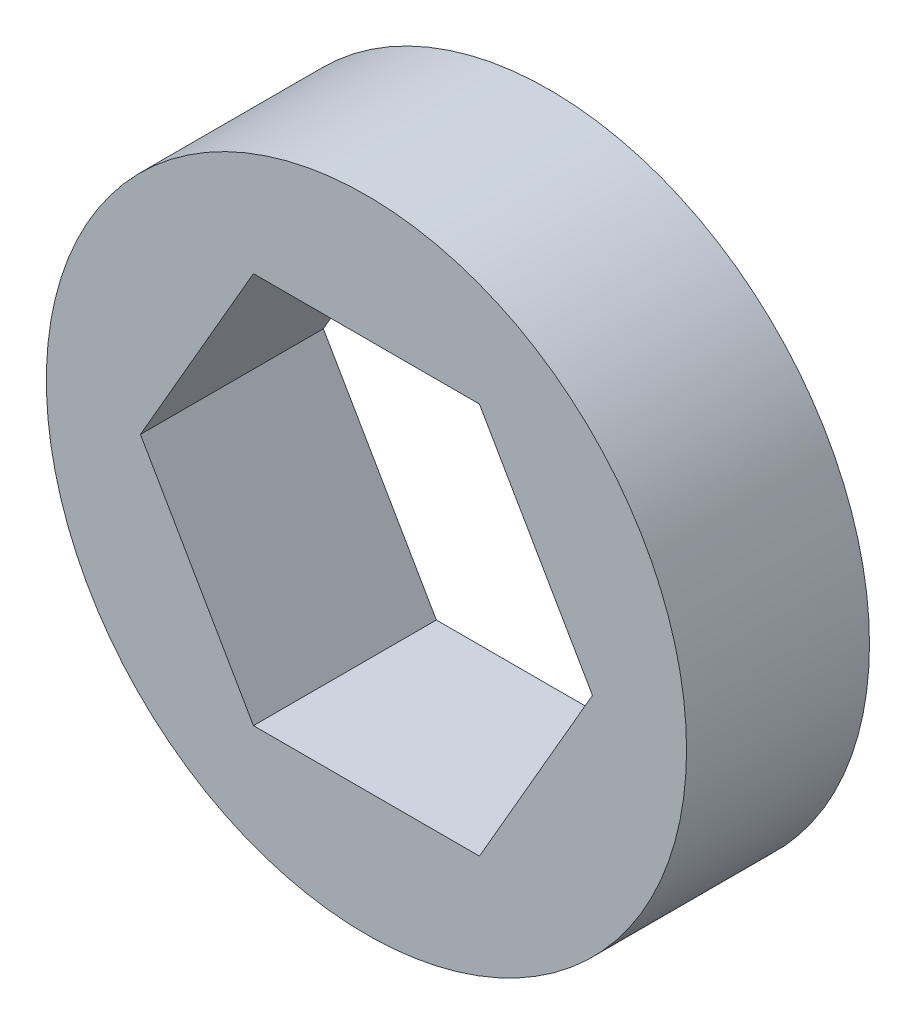
SolidWorks part; units mm, degrees
ref_plane "Front" through (0, 0, 0) normal (0, 0, 1) x (1, 0, 0)
ref_plane "Top" through (0, 0, 0) normal (0, 1, 0) x (1, 0, 0)
ref_plane "Right" through (0, 0, 0) normal (1, 0, 0) x (0, 0, -1)
sketch "Sketch1" plane through (0, 0, 0) normal (0, 0, 1) x (1, 0, 0)
  line L1 (7.8456, 0) -> (3.9228, 6.7945)
  line L2 (3.9228, 6.7945) -> (-3.9228, 6.7945)
  line L3 (-3.9228, 6.7945) -> (-7.8456, 0)
  line L4 (-7.8456, 0) -> (-3.9228, -6.7945)
  line L5 (-3.9228, -6.7945) -> (3.9228, -6.7945)
  line L6 (3.9228, -6.7945) -> (7.8456, 0)
  circle A0 centre (0, 0) radius 6.7945 construction
  circle A1 centre (0, 0) radius 11.1125
  dimension "D1" = 22.225
extrude "Boss-Extrude1" add sketch "Sketch1" along normal blind 6.35
